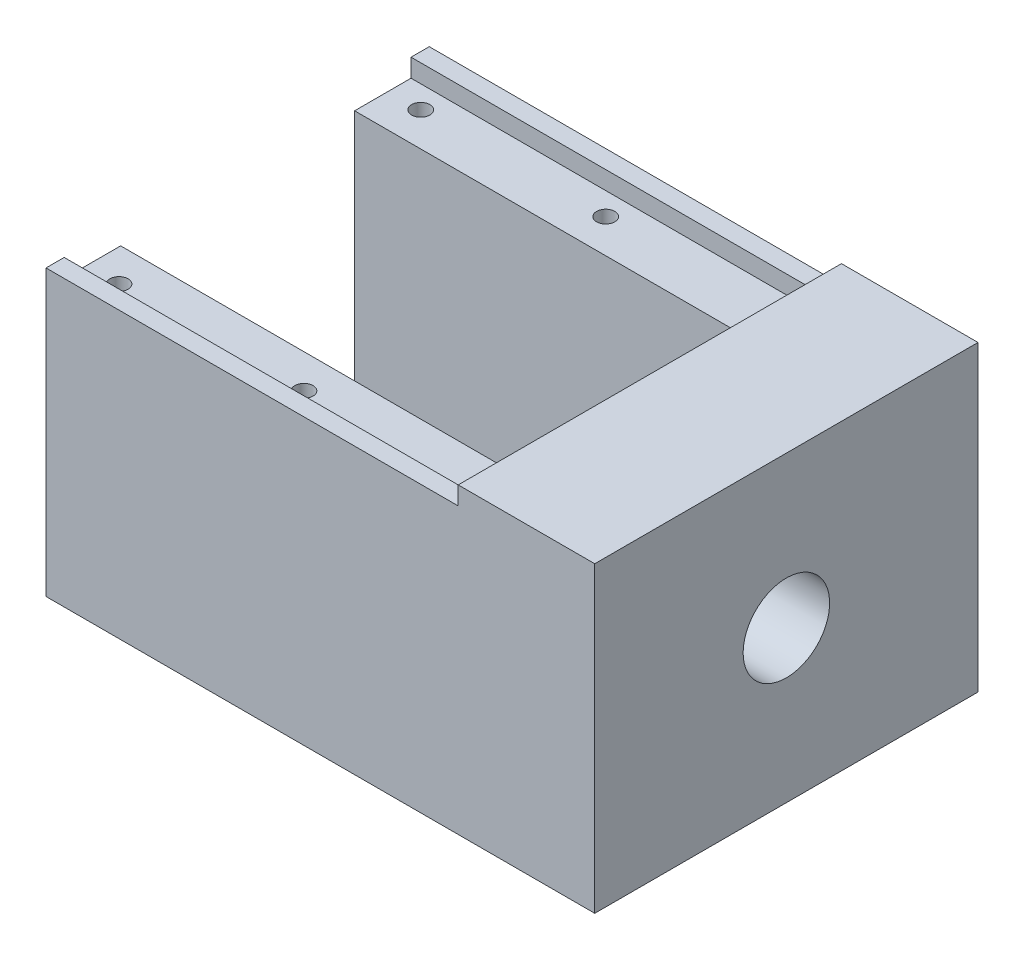
SolidWorks part; units mm, degrees
ref_plane "Front Plane" through (0, 0, 0) normal (0, 0, 1) x (1, 0, 0)
ref_plane "Top Plane" through (0, 0, 0) normal (0, 1, 0) x (1, 0, 0)
ref_plane "Right Plane" through (0, 0, 0) normal (1, 0, 0) x (0, 0, -1)
sketch "Sketch1" plane through (0, 0, 0) normal (0, 1, 0) x (1, 0, 0)
  line L1 (0, 0) -> (59.28, 0)
  line L2 (0, 0) -> (0, 38.1)
  line L3 (0, 38.1) -> (59.28, 38.1)
  line L4 (59.28, 0) -> (59.28, 38.1)
  dimension "D1" = 38.1
  dimension "D2" = 59.28
extrude "Boss-Extrude2" add sketch "Sketch1" along normal blind 29.26
sketch "Sketch2" plane through (0, 29.26, 0) normal (0, 1, 0) x (1, 0, 0)
  line L0 (59.28, 38.1) -> (0, 38.1) construction
  line L1 (59.28, 0) -> (44.28, 0)
  line L2 (59.28, 0) -> (59.28, 38.1)
  line L3 (59.28, 38.1) -> (44.28, 38.1)
  line L4 (44.28, 0) -> (44.28, 38.1)
  dimension "D1" = 15
extrude "Boss-Extrude3" add sketch "Sketch2" along normal blind 4
sketch "Sketch4" plane through (0, 29.26, 0) normal (0, 1, 0) x (1, 0, 0)
  line L0 (0, 38.1) -> (0, 0) construction
  line L1 (0, 6.2) -> (44.28, 6.2)
  line L2 (0, 6.2) -> (0, 31.9)
  line L3 (0, 31.9) -> (44.28, 31.9)
  line L4 (44.28, 6.2) -> (44.28, 31.9)
  line L5 (44.28, 38.1) -> (44.28, 0) construction
  line L6 (-44.28, 19.05) -> (44.28, 19.05) construction
  line L7 (44.28, 38.1) -> (0, 38.1) construction
  line L8 (0, 0) -> (44.28, 0) construction
  point P11 (0, 19.05)
  dimension "D1" = 0
  dimension "D2" = 25.7
extrude "Cut-Extrude7" cut sketch "Sketch4" against normal offset from surface (27.26 mm away) 2 contours L1 L4 L3 L2 up to face at (29.64, 0, -19.05)
sketch "Sketch7" plane through (59.28, 0, 0) normal (1, 0, 0) x (0, 0, -1)
  line L0 (19.05, 58.8813) -> (19.05, 7.6387) construction
  line L3 (38.1, 33.26) -> (38.1, 0) construction
  line L4 (38.1, 16.63) -> (0, 16.63) construction
  line L5 (0, 33.26) -> (0, 0) construction
  circle A0 centre (19.05, 16.63) radius 4.75
  point P5 (19.05, 33.26)
  dimension "D1" = 9.5
sketch "Sketch8" plane through (44.28, 0, 0) normal (-1, 0, 0) x (0, 0, 1)
  line L0 (-19.05, 33.26) -> (-19.05, 2) construction
  line L1 (-38.1, 33.26) -> (0, 33.26) construction
  line L2 (-6.2, 2) -> (-31.9, 2) construction
  line L3 (-31.9136, 16.5568) -> (-8.2707, 16.5568) construction
  circle A0 centre (-19.05, 16.5568) radius 4.8077
loft "Cut-Loft2" cut profiles "Sketch7", "Sketch8"
sketch "Sketch13" plane through (0, 0, 0) normal (0, 0, 1) x (1, 0, 0)
  line L2 (0, 29.26) -> (0, 0)
  line L3 (0, 0) -> (59.28, 0)
  line L4 (59.28, 29.26) -> (59.28, 0)
  line L6 (59.28, 29.26) -> (59.28, 33.26)
  line L7 (59.28, 33.26) -> (0, 33.26)
  line L8 (0, 29.26) -> (0, 33.26)
  line L9 (44.28, 33.26) -> (59.28, 33.26) construction
  dimension "D1" = 0
extrude "Boss-Extrude4" add sketch "Sketch13" along normal blind 2
sketch "Sketch14" plane through (0, 0, -38.1) normal (0, 0, -1) x (-1, 0, 0)
  line L0 (-59.28, 33.26) -> (-44.28, 33.26) construction
  line L1 (-59.28, 0) -> (0, 0)
  line L2 (-59.28, 0) -> (-59.28, 29.26)
  line L4 (0, 0) -> (0, 29.26)
  line L6 (-59.28, 29.26) -> (-59.28, 33.26)
  line L7 (-59.28, 33.26) -> (0, 33.26)
  line L8 (0, 29.26) -> (0, 33.26)
  dimension "D1" = 0
extrude "Boss-Extrude5" add sketch "Sketch14" along normal blind 2
sketch "Sketch15" plane through (0, 33.26, 0) normal (0, 1, 0) x (1, 0, 0)
  line L9 (59.28, -2) -> (0, -2) construction
  line L10 (0, 0) -> (44.28, 0)
  line L11 (0, 0) -> (0, -2)
  line L12 (0, -2) -> (44.28, -2)
  line L13 (44.28, 0) -> (44.28, -2)
  line L14 (44.28, 38.1) -> (44.28, 0) construction
  line L15 (44.28, 38.1) -> (0, 38.1)
  line L16 (44.28, 38.1) -> (44.28, 40.1)
  line L17 (44.28, 40.1) -> (0, 40.1)
  line L18 (0, 38.1) -> (0, 40.1)
  dimension "D1" = 0
extrude "Cut-Extrude9" cut sketch "Sketch15" against normal blind 2 contours L11 L10 L13 L12 | L17 L18 L15 L16
sketch "Sketch16" plane through (0, 0, 0) normal (-1, 0, 0) x (0, 0, 1)
  line L0 (-40.1, 31.26) -> (-38.1, 31.26)
  line L1 (-38.1, 31.26) -> (-38.1, 29.26)
  line L2 (-38.1, 29.26) -> (-31.9, 29.26)
  line L3 (-31.9, 29.26) -> (-31.9, 2)
  line L4 (-31.9, 2) -> (-6.2, 2)
  line L5 (-6.2, 2) -> (-6.2, 29.26)
  line L6 (-6.2, 29.26) -> (0, 29.26)
  line L7 (0, 29.26) -> (0, 31.26)
  line L8 (0, 31.26) -> (2, 31.26)
  line L9 (2, 31.26) -> (2, 0)
  line L10 (2, 0) -> (-40.1, 0)
  line L11 (-40.1, 0) -> (-40.1, 31.26)
extrude "Boss-Extrude6" add sketch "Sketch16" along normal blind 1
hole_wizard "Ø2.0mm Dowel Hole1" positions "Sketch17" profile "Sketch18" hole size "Ø2.0" standard "ANSI Metric"
sketch "Sketch17" plane through (0, 29.26, 0) normal (0, 1, 0) x (1, 0, 0)
  line L2 (-1, 0) -> (44.28, 0) construction
  line L4 (-1, 0) -> (-1, 6.2) construction
  point P0 (2.54, 2.475)
  point P2 (22.86, 2.475)
  dimension "D1" = 20.32
  dimension "D3" = 2.475
  dimension "D4" = 3.54
sketch "Sketch18" plane through (2.54, 29.26, -2.475) normal (1, 0, 0) x (0, 0, 1)
  line L0 (0, 0) -> (0, 20.6009)
  line L1 (0, 20.6009) -> (1, 20)
  line L2 (1, 20) -> (1, 0)
  line L5 (1, 0) -> (0, 0)
  line L10 (0, 20.6009) -> (-1, 20) construction
  line L11 (0, -6.35) -> (0, 107.95) construction
  dimension "Hole Dia." = 2
  dimension "Hole Depth" = 20
  dimension "Drill Angle" = 118
pattern_linear "LPattern1" count 2 spacing 33.15 along (0, 0, -1) of "Ø2.0mm Dowel Hole1"
sketch "Sketch20" plane through (44.28, 0, 0) normal (-1, 0, 0) x (0, 0, 1)
  line L1 (-26.05, 23.7168) -> (-12.05, 23.7168)
  line L2 (-26.05, 23.7168) -> (-26.05, 9.7168)
  line L3 (-26.05, 9.7168) -> (-12.05, 9.7168)
  line L4 (-12.05, 23.7168) -> (-12.05, 9.7168)
  line L8 (-31.9, 29.26) -> (-31.9, 2)
  line L9 (-31.9, 2) -> (-6.2, 2)
  line L10 (-6.2, 2) -> (-6.2, 29.26)
  line L16 (-19.05, 23.7168) -> (-19.05, 9.7168) construction
  line L17 (-26.05, 16.7168) -> (-12.05, 16.7168) construction
  line L18 (-40.1, 33.26) -> (2, 33.26) construction
  line L20 (-31.9, 29.26) -> (-6.2, 29.26)
  dimension "D1" = 14
  dimension "D2" = 14
  dimension "D3" = 16.5432
extrude "Cut-Extrude10" cut sketch "Sketch20" against normal offset from surface (11 mm away) 4 up to face at (59.28, 16.63, -23.8)
